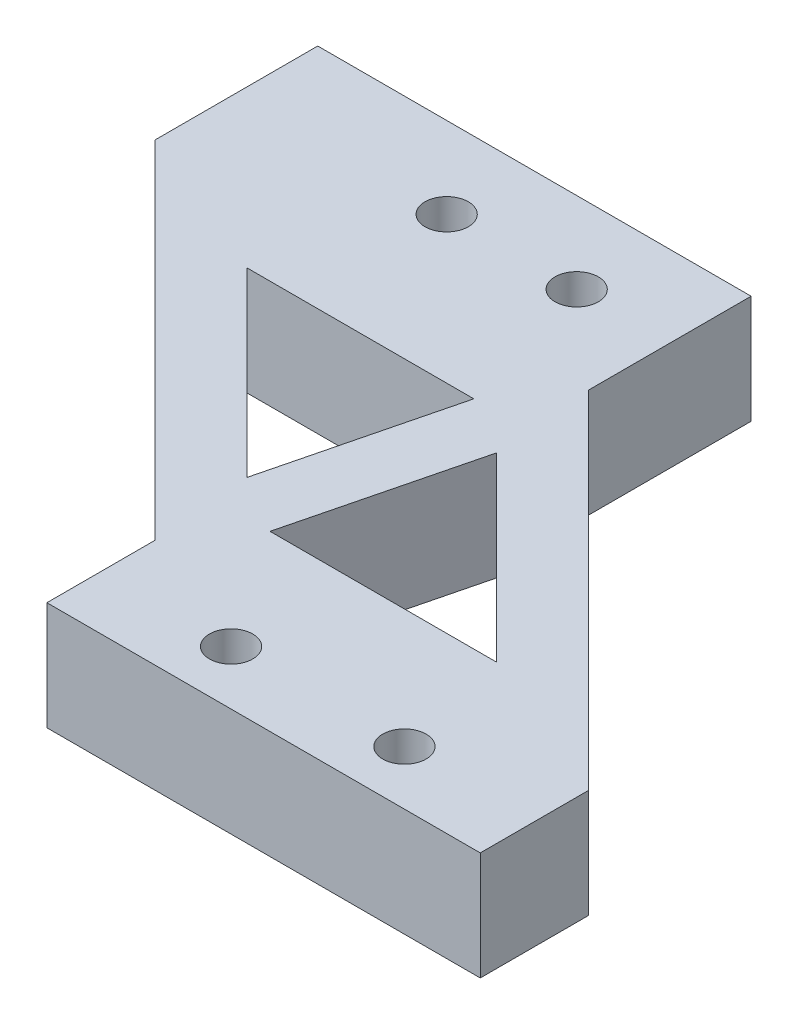
SolidWorks part; units mm, degrees
ref_plane "Front Plane" through (0, 0, 0) normal (0, 0, 1) x (1, 0, 0)
ref_plane "Top Plane" through (0, 0, 0) normal (0, 1, 0) x (1, 0, 0)
ref_plane "Right Plane" through (0, 0, 0) normal (1, 0, 0) x (0, 0, -1)
sketch "Sketch1" plane through (0, 0, 0) normal (0, 1, 0) x (1, 0, 0)
  line L0 (-37.1727, 27.4746) -> (-17.1727, 27.4746)
  line L1 (-21.1727, 11.4746) -> (-1.1727, 11.4746)
  line L2 (-17.1727, 27.4746) -> (-1.1727, 11.4746)
  line L3 (-37.1727, 27.4746) -> (-21.1727, 11.4746)
  dimension "D1" = 45
  dimension "D2" = 135
  dimension "D3" = 16
  dimension "D4" = 20
extrude "Boss-Extrude1" add sketch "Sketch1" along normal blind 5
sketch "Sketch2" plane through (0, 0, -27.4746) normal (0, 0, -1) x (-1, 0, 0)
  line L0 (17.1727, 5) -> (17.1727, 0) construction
  line L1 (37.1727, 0) -> (17.1727, 0)
  line L2 (37.1727, 0) -> (37.1727, 5)
  line L3 (37.1727, 5) -> (17.1727, 5)
  line L4 (17.1727, 0) -> (17.1727, 5)
  line L5 (17.1727, 5) -> (37.1727, 5) construction
extrude "Boss-Extrude2" add sketch "Sketch2" along normal blind 7.5
sketch "Sketch3" plane through (0, 0, -11.4746) normal (0, 0, 1) x (1, 0, 0)
  line L1 (-21.1727, 5) -> (-1.1727, 5)
  line L2 (-21.1727, 5) -> (-21.1727, 0)
  line L3 (-21.1727, 0) -> (-1.1727, 0)
  line L4 (-1.1727, 5) -> (-1.1727, 0)
extrude "Boss-Extrude3" add sketch "Sketch3" along normal blind 5
sketch "Sketch5" plane through (0, 5, 0) normal (0, 1, 0) x (1, 0, 0)
  line L0 (-17.1727, 27.4746) -> (-37.1727, 27.4746) construction
  line L1 (-37.1727, 27.4746) -> (-21.1727, 11.4746) construction
  line L2 (-17.1727, 27.4746) -> (-21.1727, 11.4746) construction
  line L3 (-1.1727, 11.4746) -> (-21.1727, 11.4746) construction
  line L4 (-16.7843, 22.8436) -> (-8.4154, 14.4746)
  line L5 (-8.4154, 14.4746) -> (-18.8766, 14.4746)
  line L6 (-16.7843, 22.8436) -> (-18.8766, 14.4746)
  line L7 (-1.1727, 11.4746) -> (-17.1727, 27.4746) construction
  line L8 (-21.5611, 16.1056) -> (-29.9301, 24.4746)
  line L9 (-29.9301, 24.4746) -> (-19.4689, 24.4746)
  line L10 (-21.5611, 16.1056) -> (-19.4689, 24.4746)
  dimension "D1" = 3
  dimension "D2" = 3
  dimension "D3" = 1.5
  dimension "D4" = 1.5
  dimension "D5" = 3
  dimension "D6" = 3
extrude "Cut-Extrude2" cut sketch "Sketch5" against normal up to next
sketch "Sketch7" plane through (0, 5, 0) normal (0, 1, 0) x (1, 0, 0)
  line L0 (-21.1727, 6.4746) -> (-21.1727, 11.4746) construction
  line L2 (-1.1727, 6.4746) -> (-21.1727, 6.4746) construction
  line L3 (-1.1727, 6.4746) -> (-1.1727, 11.4746) construction
  circle A0 centre (-15.1727, 8.9746) radius 1
  circle A1 centre (-7.1727, 8.9746) radius 1
  dimension "D4" = 2
  dimension "D5" = 2
  dimension "D6" = 6
  dimension "D1" = 6
  dimension "D2" = 2.5
  dimension "D3" = 2.5
extrude "Cut-Extrude3" cut sketch "Sketch7" against normal up to next
sketch "Sketch8" plane through (0, 5, 0) normal (0, 1, 0) x (1, 0, 0)
  line L0 (-17.1727, 34.9746) -> (-17.1727, 27.4746) construction
  line L1 (-37.1727, 34.9746) -> (-17.1727, 34.9746) construction
  circle A0 centre (-21.4727, 31.2246) radius 1
  circle A1 centre (-27.4727, 31.2246) radius 1
  dimension "D1" = 2
  dimension "D2" = 2
  dimension "D4" = 3.75
  dimension "D5" = 3.75
  dimension "D6" = 6
  dimension "D3" = 4.3
extrude "Cut-Extrude4" cut sketch "Sketch8" against normal up to next
